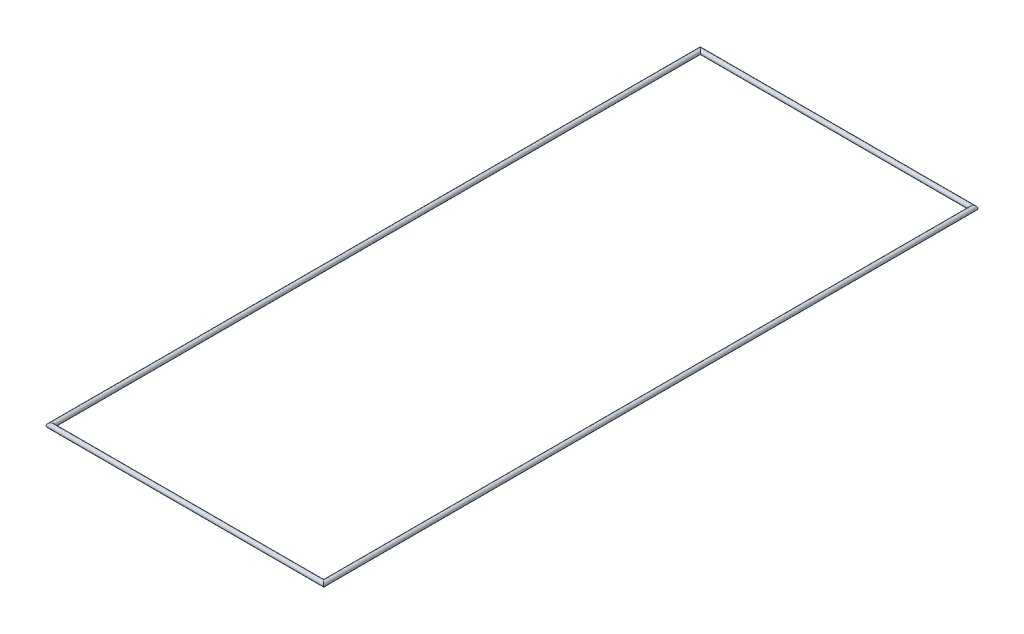
SolidWorks part; units mm, degrees
ref_plane "Front Plane" through (0, 0, 0) normal (0, 0, 1) x (1, 0, 0)
ref_plane "Top Plane" through (0, 0, 0) normal (0, 1, 0) x (1, 0, 0)
ref_plane "Right Plane" through (0, 0, 0) normal (1, 0, 0) x (0, 0, -1)
sketch "Sketch1" plane through (0, 0, 0) normal (0, 1, 0) x (1, 0, 0)
  line L6 (-29, 54) -> (-29, -84)
  line L10 (-29, -84) -> (29, -84)
  line L12 (29, -84) -> (29, 54)
  line L30 (29, 54) -> (-29, 54)
sweep "Sweep1" add path "Sketch1" circular profile diameter 1 parameters "D3"=1
